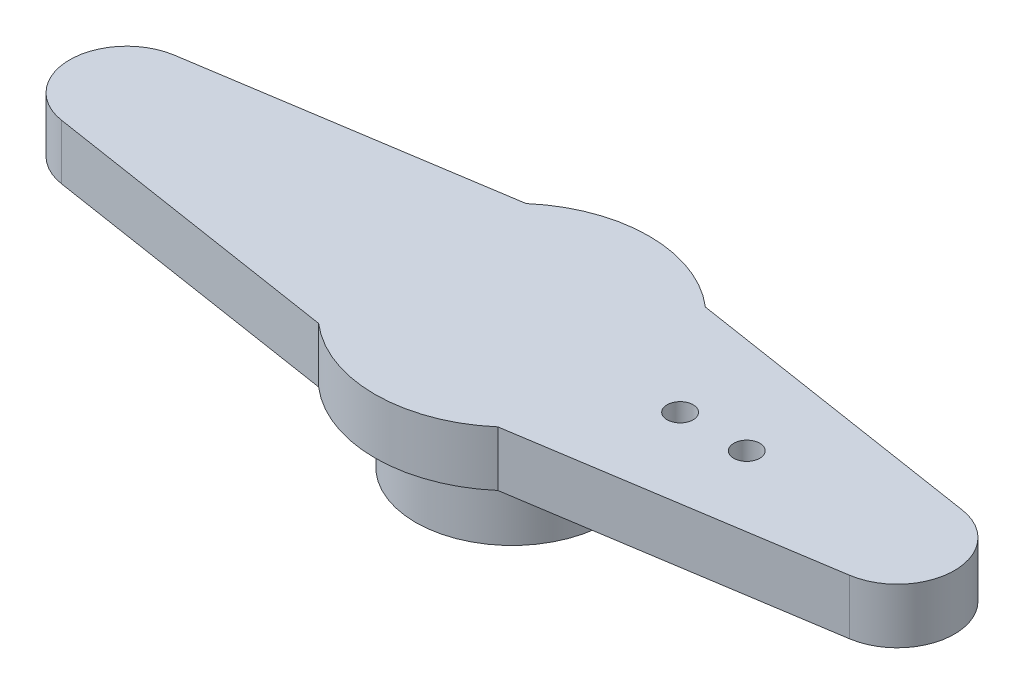
SolidWorks part; units mm, degrees
ref_plane "Front Plane" through (0, 0, 0) normal (0, 0, 1) x (1, 0, 0)
ref_plane "Top Plane" through (0, 0, 0) normal (0, 1, 0) x (1, 0, 0)
ref_plane "Right Plane" through (0, 0, 0) normal (1, 0, 0) x (0, 0, -1)
sketch "Sketch1" plane through (0, 0, 0) normal (0, 1, 0) x (1, 0, 0)
  line L0 (0, 0) -> (33.7337, 0) construction
  line L1 (0, 4.5308) -> (0, -4.5306) construction
  line L2 (3.926, 4.5466) -> (17.2648, 2.4701)
  line L3 (3.926, -4.5466) -> (17.2648, -2.4701)
  line L4 (-3.926, -4.5466) -> (-17.2648, -2.4701)
  line L5 (-3.926, 4.5466) -> (-17.2648, 2.4701)
  arc A0 (-3.926, -4.5466) -> (3.926, -4.5466) centre (0, 0) ccw
  arc A1 (17.2648, 2.4701) -> (17.2648, -2.4701) centre (16.8803, 0) cw
  arc A2 (-17.2648, 2.4701) -> (-17.2648, -2.4701) centre (-16.8803, 0) ccw
  arc A3 (3.926, 4.5466) -> (-3.926, 4.5466) centre (0, 0) ccw
  dimension "D1" = 12.0142
  dimension "D2" = 38.7604
  dimension "D3" = 9.0932
  dimension "D4" = 4.9403
extrude "Boss-Extrude1" add sketch "Sketch1" along normal blind 2.413
sketch "Sketch2" plane through (0, 0, 0) normal (0, -1, 0) x (1, 0, 0)
  circle A0 centre (0, 0) radius 2.8829
  circle A1 centre (0, 0) radius 4.2227
  dimension "D1" = 8.4455
  dimension "D2" = 5.7658
extrude "Boss-Extrude2" add sketch "Sketch2" along normal blind 3.3401
sketch "Sketch3" plane through (0, 2.413, 0) normal (0, 1, 0) x (1, 0, 0)
  line L0 (0, 2.1292) -> (0, -1.8161) construction
  circle A0 centre (7.366, 0) radius 0.5715
  circle A1 centre (10.287, 0) radius 0.5715
  dimension "D1" = 1.143
  dimension "D2" = 14.732
  dimension "D3" = 20.574
extrude "Cut-Extrude1" cut sketch "Sketch3" against normal up to next contours A0 | A1
